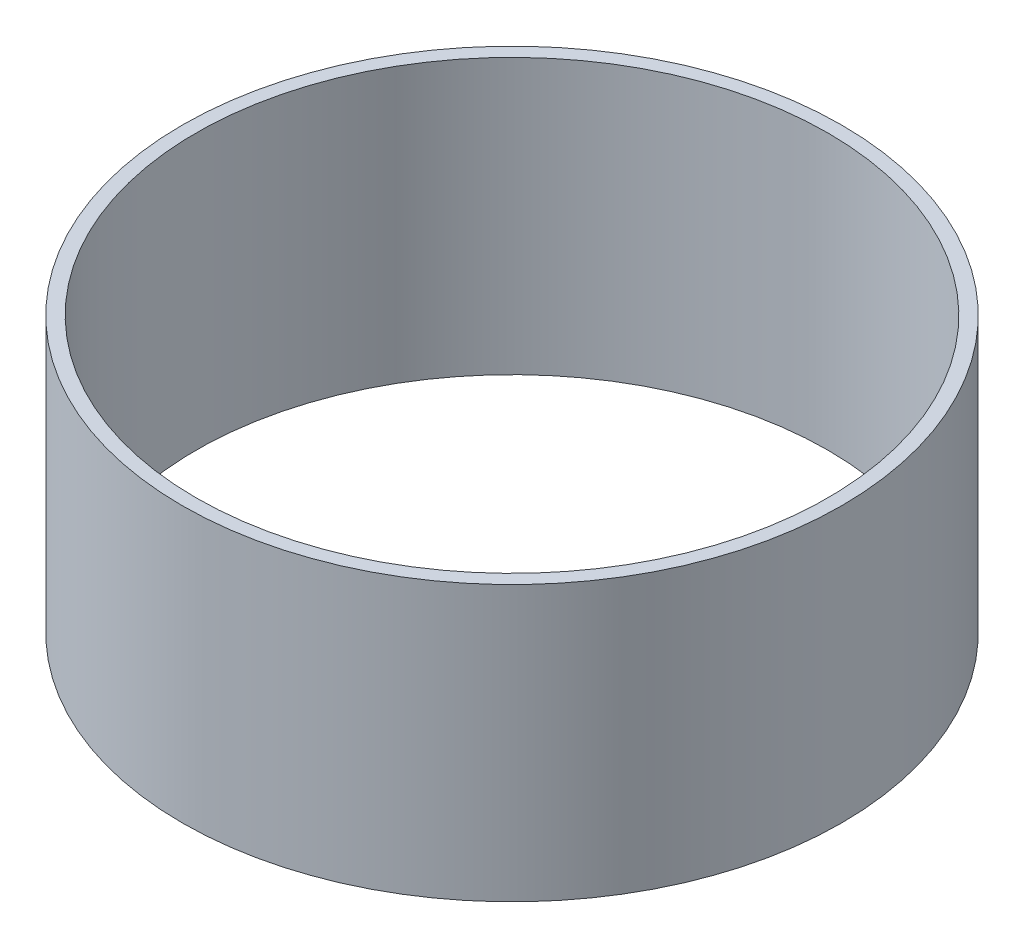
SolidWorks part; units mm, degrees
material "6061-T6 (SS)"
ref_plane "Front Plane" through (0, 0, 0) normal (0, 0, 1) x (1, 0, 0)
ref_plane "Top Plane" through (0, 0, 0) normal (0, 1, 0) x (1, 0, 0)
ref_plane "Right Plane" through (0, 0, 0) normal (1, 0, 0) x (0, 0, -1)
sketch "Sketch1" plane through (0, 0, 0) normal (0, 1, 0) x (1, 0, 0)
  circle A0 centre (0, 0) radius 152.4
  circle A1 centre (0, 0) radius 146.05
  dimension "D1" = 304.8
  dimension "D2" = 6.35
extrude "Boss-Extrude1" add sketch "Sketch1" along normal blind 127
